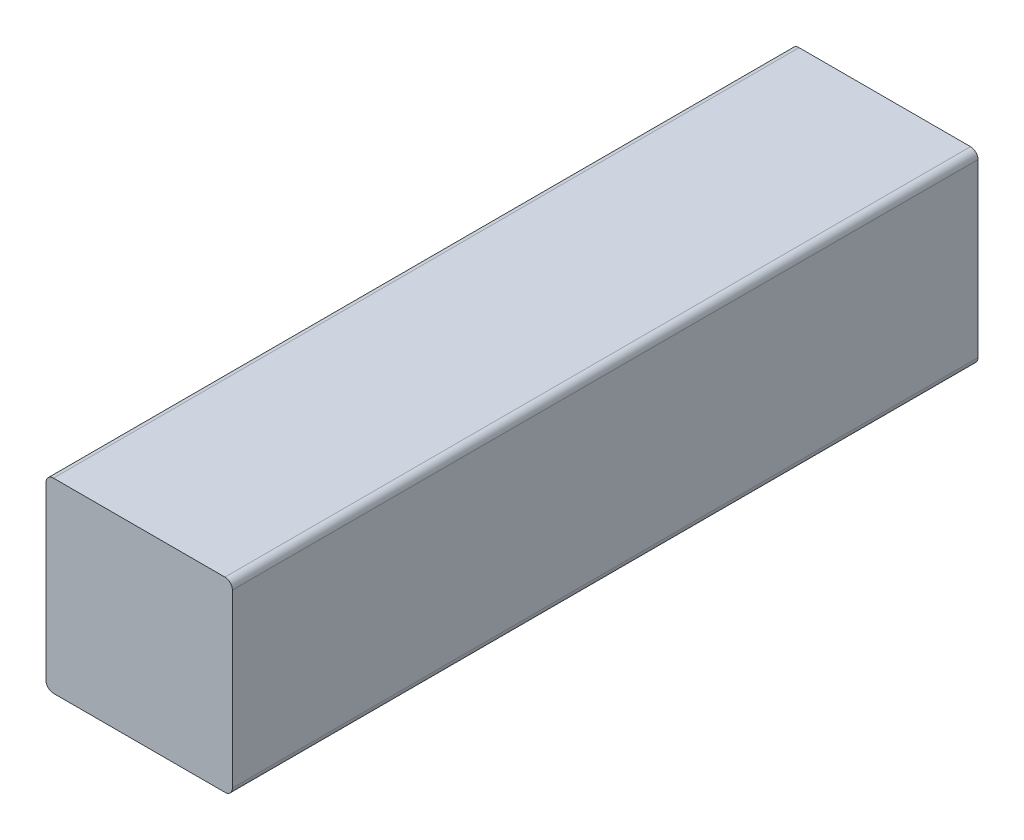
SolidWorks part; units mm, degrees
ref_plane "Front Plane" through (0, 0, 0) normal (0, 0, 1) x (1, 0, 0)
ref_plane "Top Plane" through (0, 0, 0) normal (0, 1, 0) x (1, 0, 0)
ref_plane "Right Plane" through (0, 0, 0) normal (1, 0, 0) x (0, 0, -1)
sketch "Sketch1" plane through (0, 0, 0) normal (1, 0, 0) x (0, 0, -1)
  line L0 (-12.7, 3.175) -> (12.7, 3.175) construction
  line L1 (-12.7, 3.175) -> (-12.7, -3.175) construction
  line L2 (3.4925, 0) -> (-3.4925, 0) construction
  line L3 (0, 3.4925) -> (0, -3.4925) construction
  point P2 (0, 3.175)
  point P4 (-12.7, 0)
  dimension "Height" = 6.35
  dimension "Length" = 25.4
sketch "Sketch3" plane through (0, 0, 0) normal (0, 0, 1) x (1, 0, 0)
  line L0 (-3.175, 3.175) -> (3.175, 3.175) construction
  line L1 (3.175, 3.175) -> (3.175, -3.175) construction
  line L2 (0, 3.175) -> (0, -3.175) construction
  dimension "Width" = 6.35
  dimension "Height" = 6.35
sketch "Sketch4" plane through (0, 0, 0) normal (1, 0, 0) x (0, 0, -1)
  line L0 (-12.7, -3.175) -> (-12.7, 3.175)
  line L1 (-12.7, -3.175) -> (12.7, -3.175)
  line L2 (-12.7, 3.175) -> (12.7, 3.175)
  line L3 (12.7, -3.175) -> (12.7, 3.175)
extrude "Boss-Extrude1" add sketch "Sketch4" along normal up to vertex (3.175 mm away) from vertex at -3.175 starting at point (-3.175, 3.175, 0)
fillet "Fillet1" radius 0.254 4 edges at (-3.175, -3.175, 0) (3.175, -3.175, 0) (-3.175, 3.175, 0) (3.175, 3.175, 0)
